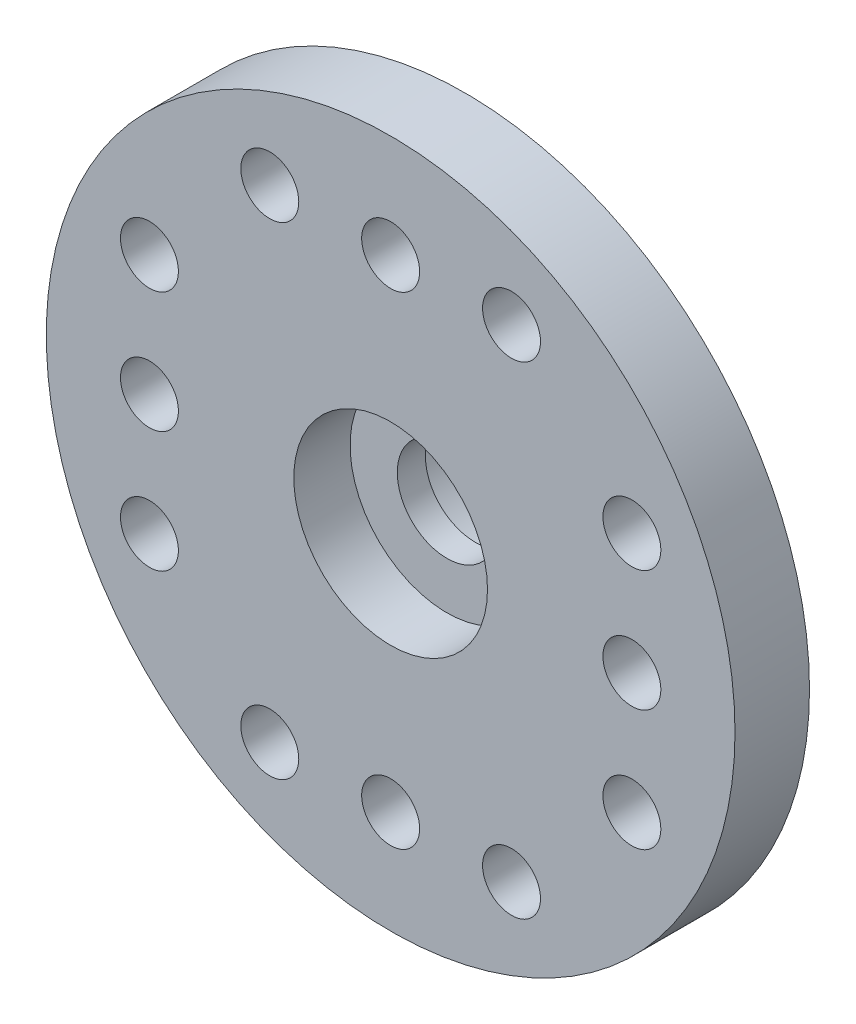
SolidWorks part; units mm, degrees
ref_plane "Front Plane" through (0, 0, 0) normal (0, 0, 1) x (1, 0, 0)
ref_plane "Top Plane" through (0, 0, 0) normal (0, 1, 0) x (1, 0, 0)
ref_plane "Right Plane" through (0, 0, 0) normal (1, 0, 0) x (0, 0, -1)
sketch "Sketch1" plane through (0, 0, 0) normal (0, 0, 1) x (1, 0, 0)
  circle A0 centre (9.62, 10) radius 10.4
  dimension "D1" = 20.8
extrude "Boss-Extrude1" add sketch "Sketch1" along normal blind 2.25 contours A0
sketch "Sketch2" plane through (0, 0, 0) normal (0, 0, -1) x (-1, 0, 0)
  circle A0 centre (-9.62, 10) radius 4.4
  dimension "D1" = 8.8
extrude "Boss-Extrude2" add sketch "Sketch2" along normal blind 3.3
sketch "Sketch3" plane through (0, 0, 2.25) normal (0, 0, 1) x (1, 0, 0)
  line L0 (9.62, 3.59) -> (9.62, 7.09) construction
  line L1 (9.62, 1.84) -> (9.62, -0.4) construction
  line L2 (8.12, 10) -> (-0.78, 10) construction
  line L3 (12.395, 2.715) -> (10.495, 2.715) construction
  line L4 (8.745, 2.715) -> (6.845, 2.715) construction
  circle A0 centre (9.62, 10) radius 1.5
  circle A1 centre (9.62, 2.715) radius 0.875
  circle A2 centre (9.62, 10) radius 10.4 construction
  circle A3 centre (9.62, 10) radius 2.91 construction
  circle A4 centre (5.97, 2.715) radius 0.875
  circle A5 centre (13.27, 2.715) radius 0.875
  circle A6 centre (2.335, 6.35) radius 0.875
  circle A7 centre (2.335, 10) radius 0.875
  circle A8 centre (2.335, 13.65) radius 0.875
  circle A9 centre (5.97, 17.285) radius 0.875
  circle A10 centre (9.62, 17.285) radius 0.875
  circle A11 centre (13.27, 17.285) radius 0.875
  circle A12 centre (16.905, 13.65) radius 0.875
  circle A13 centre (16.905, 10) radius 0.875
  circle A14 centre (16.905, 6.35) radius 0.875
  point P43 (9.62, 10)
  dimension "D1" = 3
  dimension "D2" = 1.75
  dimension "D5" = 5.82
  dimension "D3" = 3.5
  dimension "D4" = 2.24
  dimension "D6" = 1.9
  dimension "D7" = 4
extrude "Cut-Extrude1" cut sketch "Sketch3" against normal up to surface (5.55 mm away) up to face at (5.22, 10, -3.3)
sketch "Sketch4" plane through (0, 0, 2.25) normal (0, 0, 1) x (1, 0, 0)
  circle A0 centre (9.62, 10) radius 2.925
  dimension "D1" = 5.85
extrude "Cut-Extrude2" cut sketch "Sketch4" against normal blind 1.7
sketch "Sketch5" plane through (0, 0, -3.3) normal (0, 0, -1) x (-1, 0, 0)
  circle A0 centre (-9.62, 10) radius 2.95
  dimension "D1" = 5.9
extrude "Cut-Extrude3" cut sketch "Sketch5" against normal blind 3
